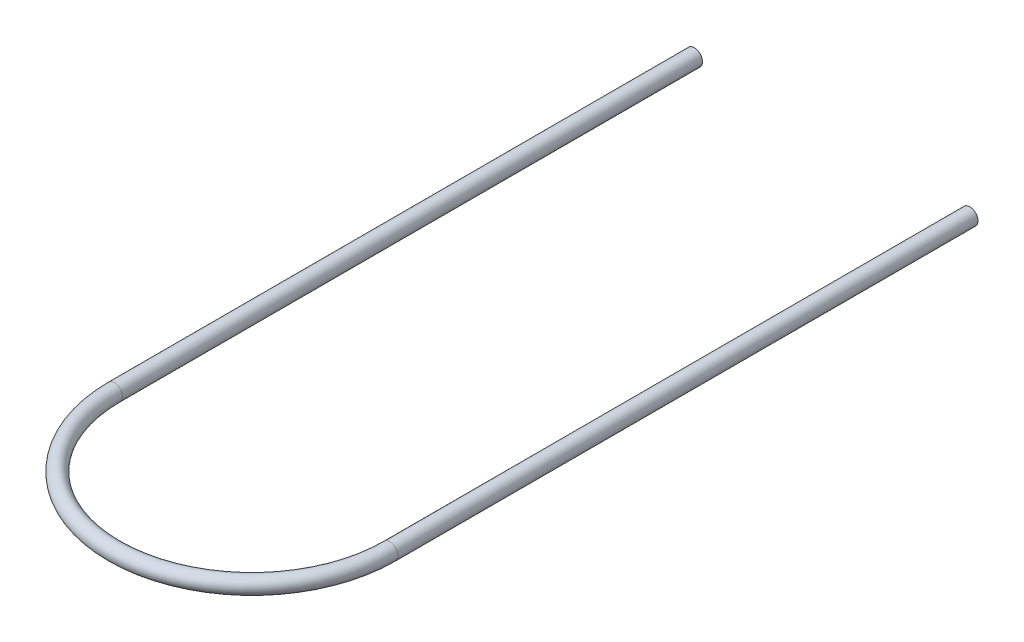
SolidWorks part; units mm, degrees
ref_plane "Front Plane" through (0, 0, 0) normal (0, 0, 1) x (1, 0, 0)
ref_plane "Top Plane" through (0, 0, 0) normal (0, 1, 0) x (1, 0, 0)
ref_plane "Right Plane" through (0, 0, 0) normal (1, 0, 0) x (0, 0, -1)
sketch "Sketch2" plane through (0, 0, 0) normal (0, 1, 0) x (1, 0, 0)
  line L0 (-241.3, 0) -> (-241.3, 1016)
  line L1 (241.3, 0) -> (241.3, 1016)
  arc A0 (-241.3, 0) -> (241.3, 0) centre (0, 0) ccw
  point P9 (0, -241.3)
  dimension "D1" = 241.3
  dimension "D2" = 1016
  dimension "D3" = 1016
sweep "Sweep3" add path "Sketch2" circular profile diameter 28.448 parameters "D3"=28.448
